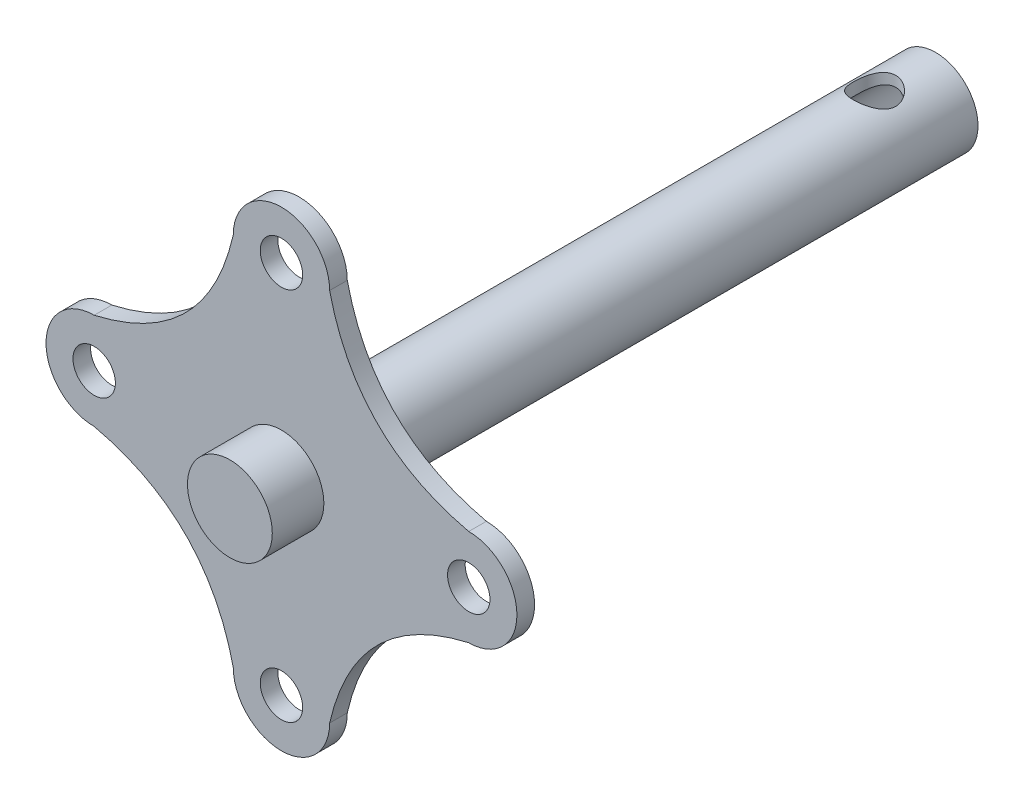
SolidWorks part; units mm, degrees
material "6061-T6 (SS)"
ref_plane "Front Plane" through (0, 0, 0) normal (0, 0, 1) x (1, 0, 0)
ref_plane "Top Plane" through (0, 0, 0) normal (0, 1, 0) x (1, 0, 0)
ref_plane "Right Plane" through (0, 0, 0) normal (1, 0, 0) x (0, 0, -1)
sketch "Sketch1" plane through (0, 0, 0) normal (0, 0, 1) x (1, 0, 0)
  line L0 (0, 0) -> (0, 44.069) construction
  line L1 (-35.052, 0) -> (35.052, 0) construction
  line L2 (0, -35.052) -> (0, 0) construction
  line L3 (0, 0) -> (17.9605, -17.9605) construction
  line L4 (0, 0) -> (-17.9605, -17.9605) construction
  line L5 (0, 0) -> (17.9605, 17.9605) construction
  line L6 (0, 0) -> (-17.9605, 17.9605) construction
  circle A0 centre (0, 35.052) radius 3.9688
  arc A1 (9.017, 35.052) -> (-9.017, 35.052) centre (0, 35.052) ccw
  arc A2 (35.052, -9.017) -> (35.052, 9.017) centre (35.052, 0) ccw
  circle A3 centre (35.052, 0) radius 3.9688
  arc A4 (-9.017, -35.052) -> (9.017, -35.052) centre (0, -35.052) ccw
  circle A5 centre (0, -35.052) radius 3.9688
  arc A6 (-35.052, 9.017) -> (-35.052, -9.017) centre (-35.052, 0) ccw
  circle A7 centre (-35.052, 0) radius 3.9688
  spline S0 degree 2 poles (-9.017, 35.052) (-13.8865, 13.8865) (-35.052, 9.017) knots 0 0 0 1 1 1
  spline S1 degree 2 poles (9.017, 35.052) (13.8865, 13.8865) (35.052, 9.017) knots 0 0 0 1 1 1
  spline S2 degree 2 poles (35.052, -9.017) (13.8865, -13.8865) (9.017, -35.052) knots 0 0 0 1 1 1
  spline S3 degree 2 poles (-35.052, -9.017) (-13.8865, -13.8865) (-9.017, -35.052) knots 0 0 0 1 1 1
  point P18 (0, 0)
  point P23 (0, 0)
  dimension "D2" = 7.9375
  dimension "D1" = 44.069
  dimension "D3" = 35.052
  dimension "D5" = 25.4
  dimension "D6" = 4
  dimension "D4" = 4
extrude "Boss-Extrude1" add sketch "Sketch1" along normal blind 3.302
sketch "Sketch2" plane through (0, 0, 3.302) normal (0, 0, 1) x (1, 0, 0)
  circle A0 centre (0, 0) radius 7.9375
  dimension "D1" = 15.875
extrude "Boss-Extrude2" add sketch "Sketch2" along normal blind 9.652
sketch "Sketch3" plane through (0, 0, 0) normal (0, 0, -1) x (-1, 0, 0)
  circle A0 centre (0, 0) radius 7.9375
  dimension "D1" = 15.875
extrude "Boss-Extrude3" add sketch "Sketch3" along normal blind 119.126
sketch "Sketch4" plane through (0, 0, -119.126) normal (0, 0, -1) x (-1, 0, 0)
  circle A0 centre (0, 0) radius 6
  dimension "D1" = 12
extrude "Cut-Extrude1" cut sketch "Sketch4" against normal blind 25.4
ref_plane "Plane1" through (0, 10.16, 0) normal (0, 1, 0) x (1, 0, 0)
sketch "Sketch5" plane through (0, 10.16, 0) normal (0, 1, 0) x (1, 0, 0)
  line L0 (0, 0) -> (0, 107.696) construction
  circle A0 centre (0, 107.696) radius 3.9687
  dimension "D2" = 7.9375
  dimension "D1" = 107.696
extrude "Cut-Extrude2" cut sketch "Sketch5" against normal up to next
